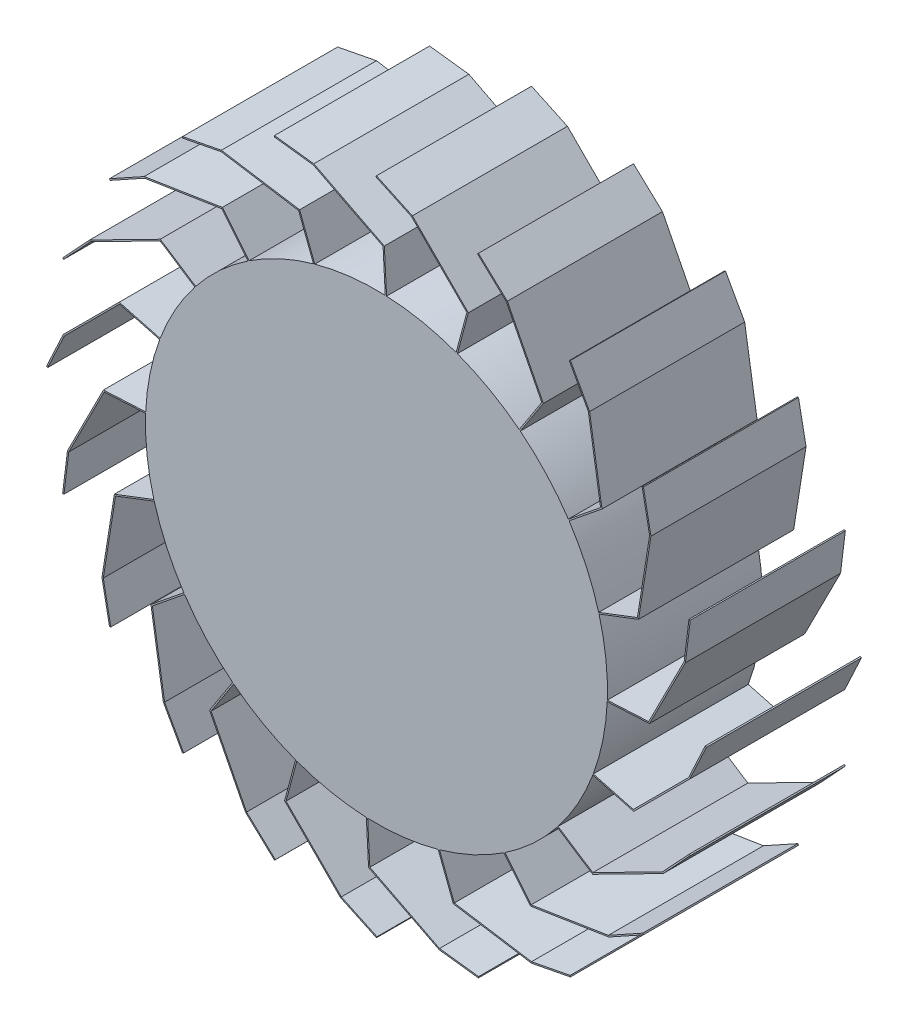
SolidWorks part; units mm, degrees
ref_plane "Front" through (0, 0, 0) normal (0, 0, 1) x (1, 0, 0)
ref_plane "Top" through (0, 0, 0) normal (0, 1, 0) x (1, 0, 0)
ref_plane "Right" through (0, 0, 0) normal (1, 0, 0) x (0, 0, -1)
sketch "Radbreite" plane through (0, 0, 0) normal (0, 1, 0) x (1, 0, 0)
  line L0 (-500, 0) -> (500, 0) construction
  line L2 (-500, -75) -> (500, -75) construction
  line L3 (-500, -75) -> (-500, 75) construction
  line L4 (-500, 75) -> (500, 75) construction
  line L5 (500, -75) -> (500, 75) construction
  line L6 (-500, -75) -> (500, 75) construction
  line L7 (-500, 75) -> (500, -75) construction
  point P0 (0, 0)
  point P4 (0, 0)
  point P10 (-500, 0)
sketch "Raddurchmesser" plane through (0, 0, 0) normal (0, 0, 1) x (1, 0, 0)
  circle A0 centre (0, 0) radius 500 construction
  circle A1 centre (0, 0) radius 350
  point P5 (0, 0)
ref_plane "Ebene1" through (0, 0, 75) normal (0, 0, 1) x (1, 0, 0)
ref_plane "Ebene2" through (0, 0, -75) normal (0, 0, -1) x (-1, 0, 0)
sketch "Schaufelschnitt" plane through (0, 0, 0) normal (0, 0, 1) x (1, 0, 0)
  line L0 (0, 500) -> (54.3785, 474.6429)
  line L1 (139.2313, 389.7901) -> (122.6253, 327.8156)
  line L2 (0, 0) -> (0, 500) construction
  line L3 (54.3785, 474.6429) -> (139.2313, 389.7901)
  line L4 (0, 0) -> (154.5085, 475.5283) construction
  line L5 (-0.8452, 498.1874) -> (53.2136, 472.9793)
  line L6 (53.2136, 472.9793) -> (137.0006, 389.1924)
  line L7 (137.0006, 389.1924) -> (120.6934, 328.3332)
  line L8 (0, 500) -> (-0.8452, 498.1874)
  line L9 (122.6253, 327.8156) -> (120.6934, 328.3332)
  line L10 (139.2313, 389.7901) -> (137.0006, 389.1924) construction
  line L11 (121.6593, 328.0744) -> (138.1159, 389.4912) construction
  line L23 (0, 0) -> (0, 500) construction
  line L61 (234.995, -415.957) -> (116.4724, -397.1849) [skipped]
  line L62 (94.9557, -468.2161) -> (-11.9651, -413.7372) [skipped]
  line L63 (154.5085, -475.5283) -> (94.9557, -468.2161) [skipped]
  line L64 (-54.3785, -474.6429) -> (-139.2313, -389.7901) [skipped]
  line L65 (0, -500) -> (-54.3785, -474.6429) [skipped]
  line L66 (-198.3897, -434.6084) -> (-252.8686, -327.6876) [skipped]
  line L67 (-154.5085, -475.5283) -> (-198.3897, -434.6084) [skipped]
  line L68 (-322.9812, -352.0313) -> (-341.7533, -233.5087) [skipped]
  line L69 (-293.8926, -404.5085) -> (-322.9812, -352.0313) [skipped]
  line L70 (-415.957, -234.995) -> (-397.1849, -116.4724) [skipped]
  line L71 (-404.5085, -293.8926) -> (-415.957, -234.995) [skipped]
  line L72 (-475.5283, -154.5085) -> (-468.2161, -94.9557) [skipped]
  line L73 (233.5087, -341.7533) -> (193.131, -291.8911) [skipped]
  line L74 (116.4724, -397.1849) -> (93.4792, -337.2857) [skipped]
  line L75 (-11.9651, -413.7372) -> (-15.323, -349.6644) [skipped]
  line L76 (-139.2313, -389.7901) -> (-122.6253, -327.8156) [skipped]
  line L77 (-252.8686, -327.6876) -> (-217.9241, -273.8778) [skipped]
  line L78 (-341.7533, -233.5087) -> (-291.8911, -193.131) [skipped]
  line L79 (-397.1849, -116.4724) -> (-337.2857, -93.4792) [skipped]
  line L80 (0, 0) -> (154.5085, -475.5283) construction
  line L81 (0, 0) -> (0, -500) construction
  line L82 (0, 0) -> (-154.5085, -475.5283) construction
  line L83 (0, 0) -> (-293.8926, -404.5085) construction
  line L84 (0, 0) -> (-404.5085, -293.8926) construction
  line L85 (0, 0) -> (-475.5283, -154.5085) construction
  line L86 (468.2161, 94.9557) -> (413.7372, -11.9651) [skipped]
  line L87 (475.5283, 154.5085) -> (468.2161, 94.9557) [skipped]
  line L88 (415.957, 234.995) -> (397.1849, 116.4724) [skipped]
  line L89 (404.5085, 293.8926) -> (415.957, 234.995) [skipped]
  line L90 (474.6429, -54.3785) -> (389.7901, -139.2313) [skipped]
  line L91 (500, 0) -> (474.6429, -54.3785) [skipped]
  line L92 (434.6084, -198.3897) -> (327.6876, -252.8686) [skipped]
  line L93 (475.5283, -154.5085) -> (434.6084, -198.3897) [skipped]
  line L94 (352.0313, -322.9812) -> (233.5087, -341.7533) [skipped]
  line L95 (404.5085, -293.8926) -> (352.0313, -322.9812) [skipped]
  line L96 (293.8926, -404.5085) -> (234.995, -415.957) [skipped]
  line L97 (341.7533, 233.5087) -> (291.8911, 193.131) [skipped]
  line L98 (397.1849, 116.4724) -> (337.2857, 93.4792) [skipped]
  line L99 (413.7372, -11.9651) -> (349.6644, -15.323) [skipped]
  line L100 (389.7901, -139.2313) -> (327.8156, -122.6253) [skipped]
  line L101 (327.6876, -252.8686) -> (273.8778, -217.9241) [skipped]
  line L102 (0, 0) -> (404.5085, 293.8926) construction
  line L103 (0, 0) -> (475.5283, 154.5085) construction
  line L104 (0, 0) -> (500, 0) construction
  line L105 (0, 0) -> (475.5283, -154.5085) construction
  line L106 (0, 0) -> (404.5085, -293.8926) construction
  line L107 (0, 0) -> (293.8926, -404.5085) construction
  line L108 (198.3897, 434.6084) -> (252.8686, 327.6876) [skipped]
  line L109 (154.5085, 475.5283) -> (198.3897, 434.6084) [skipped]
  line L110 (322.9812, 352.0313) -> (341.7533, 233.5087) [skipped]
  line L111 (293.8926, 404.5085) -> (322.9812, 352.0313) [skipped]
  line L112 (252.8686, 327.6876) -> (217.9241, 273.8778) [skipped]
  line L113 (-468.2161, -94.9557) -> (-413.7372, 11.9651) [skipped]
  line L114 (-413.7372, 11.9651) -> (-349.6644, 15.323) [skipped]
  line L115 (0, 0) -> (293.8926, 404.5085) construction
  line L116 (-474.6429, 54.3785) -> (-389.7901, 139.2313) [skipped]
  line L117 (-500, 0) -> (-474.6429, 54.3785) [skipped]
  line L118 (-389.7901, 139.2313) -> (-327.8156, 122.6253) [skipped]
  line L119 (-434.6084, 198.3897) -> (-327.6876, 252.8686) [skipped]
  line L120 (-475.5283, 154.5085) -> (-434.6084, 198.3897) [skipped]
  line L121 (-327.6876, 252.8686) -> (-273.8778, 217.9241) [skipped]
  line L122 (-352.0313, 322.9812) -> (-233.5087, 341.7533) [skipped]
  line L123 (-404.5085, 293.8926) -> (-352.0313, 322.9812) [skipped]
  line L124 (-233.5087, 341.7533) -> (-193.131, 291.8911) [skipped]
  line L125 (-234.995, 415.957) -> (-116.4724, 397.1849) [skipped]
  line L126 (-293.8926, 404.5085) -> (-234.995, 415.957) [skipped]
  line L127 (-116.4724, 397.1849) -> (-93.4792, 337.2857) [skipped]
  line L128 (-154.5085, 475.5283) -> (-94.9557, 468.2161) [skipped]
  line L129 (0, 0) -> (-404.5085, 293.8926) construction
  line L130 (0, 0) -> (-293.8926, 404.5085) construction
  line L131 (0, 0) -> (-475.5283, 154.5085) construction
  line L132 (0, 0) -> (-500, 0) construction
  line L133 (-94.9557, 468.2161) -> (11.9651, 413.7372) [skipped]
  line L134 (11.9651, 413.7372) -> (15.323, 349.6644) [skipped]
  line L135 (0, 0) -> (-154.5085, 475.5283) construction
  circle A0 centre (0, 0) radius 500 construction
  circle A1 centre (0, 0) radius 350 construction
sketch "Schaufelanordnung" plane through (0, 0, 0) normal (0, 0, 1) x (1, 0, 0)
  line L0 (139.2313, 389.7901) -> (122.6253, 327.8156) construction
  line L1 (0, 500) -> (54.3785, 474.6429) construction
  line L2 (54.3785, 474.6429) -> (139.2313, 389.7901) construction
  line L3 (139.2313, 389.7901) -> (122.6253, 327.8156)
  line L4 (0, 500) -> (54.3785, 474.6429)
  line L5 (54.3785, 474.6429) -> (139.2313, 389.7901)
  line L6 (252.8686, 327.6876) -> (217.9241, 273.8778)
  line L7 (198.3897, 434.6084) -> (252.8686, 327.6876)
  line L8 (154.5085, 475.5283) -> (198.3897, 434.6084)
  line L9 (341.7533, 233.5087) -> (291.8911, 193.131)
  line L10 (322.9812, 352.0313) -> (341.7533, 233.5087)
  line L11 (293.8926, 404.5085) -> (322.9812, 352.0313)
  line L12 (397.1849, 116.4724) -> (337.2857, 93.4792)
  line L13 (415.957, 234.995) -> (397.1849, 116.4724)
  line L14 (404.5085, 293.8926) -> (415.957, 234.995)
  line L15 (413.7372, -11.9651) -> (349.6644, -15.323)
  line L16 (468.2161, 94.9557) -> (413.7372, -11.9651)
  line L17 (475.5283, 154.5085) -> (468.2161, 94.9557)
  line L18 (389.7901, -139.2313) -> (327.8156, -122.6253)
  line L19 (474.6429, -54.3785) -> (389.7901, -139.2313)
  line L20 (500, 0) -> (474.6429, -54.3785)
  line L21 (327.6876, -252.8686) -> (273.8778, -217.9241)
  line L22 (434.6084, -198.3897) -> (327.6876, -252.8686)
  line L23 (475.5283, -154.5085) -> (434.6084, -198.3897)
  line L24 (233.5087, -341.7533) -> (193.131, -291.8911)
  line L25 (352.0313, -322.9812) -> (233.5087, -341.7533)
  line L26 (404.5085, -293.8926) -> (352.0313, -322.9812)
  line L27 (116.4724, -397.1849) -> (93.4792, -337.2857)
  line L28 (234.995, -415.957) -> (116.4724, -397.1849)
  line L29 (293.8926, -404.5085) -> (234.995, -415.957)
  line L30 (-11.9651, -413.7372) -> (-15.323, -349.6644)
  line L31 (94.9557, -468.2161) -> (-11.9651, -413.7372)
  line L32 (154.5085, -475.5283) -> (94.9557, -468.2161)
  line L33 (-139.2313, -389.7901) -> (-122.6253, -327.8156)
  line L34 (-54.3785, -474.6429) -> (-139.2313, -389.7901)
  line L35 (0, -500) -> (-54.3785, -474.6429)
  line L36 (-252.8686, -327.6876) -> (-217.9241, -273.8778)
  line L37 (-198.3897, -434.6084) -> (-252.8686, -327.6876)
  line L38 (-154.5085, -475.5283) -> (-198.3897, -434.6084)
  line L39 (-341.7533, -233.5087) -> (-291.8911, -193.131)
  line L40 (-322.9812, -352.0313) -> (-341.7533, -233.5087)
  line L41 (-293.8926, -404.5085) -> (-322.9812, -352.0313)
  line L42 (-397.1849, -116.4724) -> (-337.2857, -93.4792)
  line L43 (-415.957, -234.995) -> (-397.1849, -116.4724)
  line L44 (-404.5085, -293.8926) -> (-415.957, -234.995)
  line L45 (-413.7372, 11.9651) -> (-349.6644, 15.323)
  line L46 (-468.2161, -94.9557) -> (-413.7372, 11.9651)
  line L47 (-475.5283, -154.5085) -> (-468.2161, -94.9557)
  line L48 (-389.7901, 139.2313) -> (-327.8156, 122.6253)
  line L49 (-474.6429, 54.3785) -> (-389.7901, 139.2313)
  line L50 (-500, 0) -> (-474.6429, 54.3785)
  line L51 (-327.6876, 252.8686) -> (-273.8778, 217.9241)
  line L52 (-434.6084, 198.3897) -> (-327.6876, 252.8686)
  line L53 (-475.5283, 154.5085) -> (-434.6084, 198.3897)
  line L54 (-233.5087, 341.7533) -> (-193.131, 291.8911)
  line L55 (-352.0313, 322.9812) -> (-233.5087, 341.7533)
  line L56 (-404.5085, 293.8926) -> (-352.0313, 322.9812)
  line L57 (-116.4724, 397.1849) -> (-93.4792, 337.2857)
  line L58 (-234.995, 415.957) -> (-116.4724, 397.1849)
  line L59 (-293.8926, 404.5085) -> (-234.995, 415.957)
  line L60 (11.9651, 413.7372) -> (15.323, 349.6644)
  line L61 (-94.9557, 468.2161) -> (11.9651, 413.7372)
  line L62 (-154.5085, 475.5283) -> (-94.9557, 468.2161)
  line L63 (122.6253, 327.8156) -> (120.6934, 328.3332) construction
  line L64 (137.0006, 389.1924) -> (120.6934, 328.3332) construction
  line L65 (53.2136, 472.9793) -> (137.0006, 389.1924) construction
  line L66 (-0.8452, 498.1874) -> (53.2136, 472.9793) construction
  line L67 (0, 500) -> (-0.8452, 498.1874) construction
  line L68 (122.6253, 327.8156) -> (120.6934, 328.3332)
  line L69 (137.0006, 389.1924) -> (120.6934, 328.3332)
  line L70 (53.2136, 472.9793) -> (137.0006, 389.1924)
  line L71 (-0.8452, 498.1874) -> (53.2136, 472.9793)
  line L72 (0, 500) -> (-0.8452, 498.1874)
  line L73 (154.5085, 475.5283) -> (153.1445, 474.0656)
  line L74 (153.1445, 474.0656) -> (196.7678, 433.3862)
  line L75 (196.7678, 433.3862) -> (250.5623, 327.8084)
  line L76 (250.5623, 327.8084) -> (216.2468, 274.9671)
  line L78 (293.8926, 404.5085) -> (292.1434, 403.5389)
  line L79 (292.1434, 403.5389) -> (321.061, 351.3701)
  line L80 (321.061, 351.3701) -> (339.5973, 234.3363)
  line L81 (339.5973, 234.3363) -> (290.6324, 194.6853)
  line L83 (404.5085, 293.8926) -> (402.5452, 293.511)
  line L84 (402.5452, 293.511) -> (413.9265, 234.9596)
  line L85 (413.9265, 234.9596) -> (395.3902, 117.9257)
  line L86 (395.3902, 117.9257) -> (336.5689, 95.3464)
  line L88 (475.5283, 154.5085) -> (473.5432, 154.7522)
  line L89 (473.5432, 154.7522) -> (466.274, 95.5495)
  line L90 (466.274, 95.5495) -> (412.4794, -10.0282)
  line L91 (412.4794, -10.0282) -> (349.5597, -13.3257)
  line L93 (500, 0) -> (498.1874, 0.8452)
  line L94 (498.1874, 0.8452) -> (472.9793, -53.2136)
  line L95 (472.9793, -53.2136) -> (389.1924, -137.0006)
  line L96 (389.1924, -137.0006) -> (328.3332, -120.6934)
  line L98 (475.5283, -154.5085) -> (474.0656, -153.1445)
  line L99 (474.0656, -153.1445) -> (433.3862, -196.7678)
  line L100 (433.3862, -196.7678) -> (327.8084, -250.5623)
  line L101 (327.8084, -250.5623) -> (274.9671, -216.2468)
  line L103 (404.5085, -293.8926) -> (403.5389, -292.1434)
  line L104 (403.5389, -292.1434) -> (351.3701, -321.061)
  line L105 (351.3701, -321.061) -> (234.3363, -339.5973)
  line L106 (234.3363, -339.5973) -> (194.6853, -290.6324)
  line L108 (293.8926, -404.5085) -> (293.511, -402.5452)
  line L109 (293.511, -402.5452) -> (234.9596, -413.9265)
  line L110 (234.9596, -413.9265) -> (117.9257, -395.3902)
  line L111 (117.9257, -395.3902) -> (95.3464, -336.5689)
  line L113 (154.5085, -475.5283) -> (154.7522, -473.5432)
  line L114 (154.7522, -473.5432) -> (95.5495, -466.274)
  line L115 (95.5495, -466.274) -> (-10.0282, -412.4794)
  line L116 (-10.0282, -412.4794) -> (-13.3257, -349.5597)
  line L118 (0, -500) -> (0.8452, -498.1874)
  line L119 (0.8452, -498.1874) -> (-53.2136, -472.9793)
  line L120 (-53.2136, -472.9793) -> (-137.0006, -389.1924)
  line L121 (-137.0006, -389.1924) -> (-120.6934, -328.3332)
  line L123 (-154.5085, -475.5283) -> (-153.1445, -474.0656)
  line L124 (-153.1445, -474.0656) -> (-196.7678, -433.3862)
  line L125 (-196.7678, -433.3862) -> (-250.5623, -327.8084)
  line L126 (-250.5623, -327.8084) -> (-216.2468, -274.9671)
  line L128 (-293.8926, -404.5085) -> (-292.1434, -403.5389)
  line L129 (-292.1434, -403.5389) -> (-321.061, -351.3701)
  line L130 (-321.061, -351.3701) -> (-339.5973, -234.3363)
  line L131 (-339.5973, -234.3363) -> (-290.6324, -194.6853)
  line L133 (-404.5085, -293.8926) -> (-402.5452, -293.511)
  line L134 (-402.5452, -293.511) -> (-413.9265, -234.9596)
  line L135 (-413.9265, -234.9596) -> (-395.3902, -117.9257)
  line L136 (-395.3902, -117.9257) -> (-336.5689, -95.3464)
  line L138 (-475.5283, -154.5085) -> (-473.5432, -154.7522)
  line L139 (-473.5432, -154.7522) -> (-466.274, -95.5495)
  line L140 (-466.274, -95.5495) -> (-412.4794, 10.0282)
  line L141 (-412.4794, 10.0282) -> (-349.5597, 13.3257)
  line L143 (-500, 0) -> (-498.1874, -0.8452)
  line L144 (-498.1874, -0.8452) -> (-472.9793, 53.2136)
  line L145 (-472.9793, 53.2136) -> (-389.1924, 137.0006)
  line L146 (-389.1924, 137.0006) -> (-328.3332, 120.6934)
  line L148 (-475.5283, 154.5085) -> (-474.0656, 153.1445)
  line L149 (-474.0656, 153.1445) -> (-433.3862, 196.7678)
  line L150 (-433.3862, 196.7678) -> (-327.8084, 250.5623)
  line L151 (-327.8084, 250.5623) -> (-274.9671, 216.2468)
  line L153 (-404.5085, 293.8926) -> (-403.5389, 292.1434)
  line L154 (-403.5389, 292.1434) -> (-351.3701, 321.061)
  line L155 (-351.3701, 321.061) -> (-234.3363, 339.5973)
  line L156 (-234.3363, 339.5973) -> (-194.6853, 290.6324)
  line L158 (-293.8926, 404.5085) -> (-293.511, 402.5452)
  line L159 (-293.511, 402.5452) -> (-234.9596, 413.9265)
  line L160 (-234.9596, 413.9265) -> (-117.9257, 395.3902)
  line L161 (-117.9257, 395.3902) -> (-95.3464, 336.5689)
  line L163 (-154.5085, 475.5283) -> (-154.7522, 473.5432)
  line L164 (-154.7522, 473.5432) -> (-95.5495, 466.274)
  line L165 (-95.5495, 466.274) -> (10.0282, 412.4794)
  line L166 (10.0282, 412.4794) -> (13.3257, 349.5597)
  line L168 (121.6593, 328.0744) -> (138.1159, 389.4912) construction
  line L169 (121.6593, 328.0744) -> (138.1159, 389.4912) construction
  line L170 (217.0855, 274.4225) -> (251.7155, 327.748) construction
  line L171 (291.2618, 193.9082) -> (340.6753, 233.9225) construction
  line L172 (336.9273, 94.4128) -> (396.2875, 117.1991) construction
  line L173 (349.6121, -14.3243) -> (413.1083, -10.9966) construction
  line L174 (328.0744, -121.6593) -> (389.4912, -138.1159) construction
  line L175 (274.4225, -217.0855) -> (327.748, -251.7155) construction
  line L176 (193.9082, -291.2618) -> (233.9225, -340.6753) construction
  line L177 (94.4128, -336.9273) -> (117.1991, -396.2875) construction
  line L178 (-14.3243, -349.6121) -> (-10.9966, -413.1083) construction
  line L179 (-121.6593, -328.0744) -> (-138.1159, -389.4912) construction
  line L180 (-217.0855, -274.4225) -> (-251.7155, -327.748) construction
  line L181 (-291.2618, -193.9082) -> (-340.6753, -233.9225) construction
  line L182 (-336.9273, -94.4128) -> (-396.2875, -117.1991) construction
  line L183 (-349.6121, 14.3243) -> (-413.1083, 10.9966) construction
  line L184 (-328.0744, 121.6593) -> (-389.4912, 138.1159) construction
  line L185 (-274.4225, 217.0855) -> (-327.748, 251.7155) construction
  line L186 (-193.9082, 291.2618) -> (-233.9225, 340.6753) construction
  line L187 (-94.4128, 336.9273) -> (-117.1991, 396.2875) construction
  line L188 (14.3243, 349.6121) -> (10.9966, 413.1083) construction
  circle A0 centre (0, 0) radius 500 construction
  circle A1 centre (0, 0) radius 350 construction
  circle A2 centre (0, 0) radius 350
sketch "_Schottblechschnitt" plane through (0, 0, 0) normal (0, 0, 1) x (1, 0, 0)
  line L0 (14.3243, 349.6121) -> (10.9966, 413.1083) construction
  line L1 (15.3181, 349.6654) -> (121.448, 328.2544) construction
  line L2 (0, 0) -> (15.323, 349.6644) construction
  line L3 (-500, 0) -> (500, 0) construction
  line L4 (0, 0) -> (349.6644, -15.323) construction
  line L5 (121.6593, 328.0744) -> (138.1159, 389.4912) construction
  line L6 (14.9226, 347.7049) -> (121.0524, 326.2939) construction
  line L7 (0, 348.0917) -> (14.0677, 349.7179)
  line L8 (0, 0) -> (0, 500) construction
  line L9 (0, 348.0917) -> (0.2297, 346.105)
  line L10 (0.2297, 346.105) -> (14.2974, 347.7312)
  line L11 (108.1559, 332.8698) -> (107.5663, 331.0549) construction
  line L12 (0, 0) -> (154.5085, 475.5283) construction
  line L13 (0, 348.0917) -> (0, 350) construction
  line L14 (107.5663, 331.0549) -> (107.1707, 329.0944)
  line L15 (107.5663, 331.0549) -> (15.323, 349.6644)
  line L16 (14.9226, 347.7049) -> (107.1707, 329.0944)
  line L17 (134.8704, 306.085) -> (134.2514, 304.1832)
  line L18 (134.8704, 306.085) -> (148.3363, 301.7015)
  line L19 (134.2514, 304.1832) -> (147.7172, 299.7997)
  line L20 (225.5546, 245.7764) -> (149.4551, 301.1298)
  line L21 (148.2746, 299.5154) -> (224.3782, 244.159)
  line L22 (225.5546, 245.7764) -> (224.3782, 244.159)
  line L23 (239.9709, 211.7002) -> (238.6157, 210.2293)
  line L24 (239.9709, 211.7002) -> (250.3855, 202.1043)
  line L25 (238.6157, 210.2293) -> (249.0303, 200.6335)
  line L26 (297.2776, 119.0898) -> (251.1643, 201.1184)
  line L27 (249.4185, 200.1427) -> (295.5342, 118.1097)
  line L28 (297.2776, 119.0898) -> (295.5342, 118.1097)
  line L29 (296.1837, 82.1057) -> (294.3389, 81.3334)
  line L30 (296.1837, 82.1057) -> (301.6527, 69.043)
  line L31 (294.3389, 81.3334) -> (299.8078, 68.2706)
  line L32 (309.689, -25.9607) -> (301.9498, 67.8222)
  line L33 (299.9562, 67.6627) -> (307.6958, -26.1252)
  line L34 (309.689, -25.9607) -> (307.6958, -26.1252)
  line L35 (293.2838, -59.1253) -> (291.2849, -59.0587)
  line L36 (293.2838, -59.1253) -> (292.8123, -73.2788)
  line L37 (291.2849, -59.0587) -> (290.8134, -73.2122)
  line L38 (260.5311, -162.9906) -> (292.5738, -74.5123)
  line L39 (290.695, -73.8266) -> (258.6506, -162.3096)
  line L40 (260.5311, -162.9906) -> (258.6506, -162.3096)
  circle A0 centre (0, 0) radius 350 construction
  arc A1 (121.448, 328.2544) -> (124.0412, 326.4657) centre (120.6569, 324.3334) cw construction
  arc A2 (14.0677, 349.7179) -> (15.3181, 349.6654) centre (14.527, 345.7444) cw
  arc A3 (14.2974, 347.7312) -> (14.9226, 347.7049) centre (14.527, 345.7444) cw
  arc A4 (147.7172, 299.7997) -> (148.2746, 299.5154) centre (147.0982, 297.898) cw
  arc A5 (148.3363, 301.7015) -> (149.4511, 301.1327) centre (147.0982, 297.898) cw
  arc A6 (249.0303, 200.6335) -> (249.4185, 200.1427) centre (247.6751, 199.1626) cw
  arc A7 (250.3855, 202.1043) -> (251.1619, 201.1228) centre (247.6751, 199.1626) cw
  arc A8 (299.8078, 68.2706) -> (299.9562, 67.6627) centre (297.963, 67.4982) cw
  arc A9 (301.6527, 69.043) -> (301.9494, 67.8272) centre (297.963, 67.4982) cw
  arc A10 (290.8134, -73.2122) -> (290.695, -73.8266) centre (288.8145, -73.1456) cw
  arc A11 (292.8123, -73.2788) -> (292.5755, -74.5076) centre (288.8145, -73.1456) cw
  point P0 (122.6253, 327.8156)
  point P2 (15.323, 349.6644)
  point P4 (0, 0)
  point P27 (-10.1744, -10.348)
  point P40 (-23.7354, -15.5153)
  point P62 (-38.2161, -14.562)
  point P73 (-50.9825, -7.6615)
extrude "Aufsatz-Linear austragen1" add sketch "Raddurchmesser" along normal mid plane 235
extrude "Aufsatz-Linear austragen2" add sketch "Schaufelschnitt" along normal mid plane 235 contours L9 L1 L3 L0 L8 L5 L6 L7
pattern_circular "Kreismuster1" count 20 over 360 about axis through (0, 0, 0) along (0, 0, 1) of "Aufsatz-Linear austragen2"
equation "\"Durchmesser\"= 1000mm"
equation "\"Breite\"= 150mm"
equation "\"XX@Radbreite\" = \"Durchmesser\""
equation "\"D1@Radbreite\" = \"Breite\""
equation "\"D1@Raddurchmesser\" = \"Durchmesser\""
equation "\"Innenkreis\"= 700mm"
equation "\"D2@Raddurchmesser\" = \"Innenkreis\""
equation "\"Schaufelzahl\"= 20"
equation "\"Vollkreis\"= 360grad"
equation "\"SW1\"= 65grad'Schaufelwinkel aussen"
equation "\"SW2\"= 160grad'Schaufelwinkel mitte"
equation "\"SW3\"= 120grad'Schaufelwinkel innen"
equation "\"D3@Schaufelschnitt\" = \"SW2\""
equation "\"D4@Schaufelschnitt\" = \"SW3\""
equation "\"SL1\"= 60mm'Schaufellänge aussen"
equation "\"SL2\"= 120mm'Schaufellänge mitte"
equation "\"SL3\"= 30mm'Schaufellänge innen"
equation "\"D5@Schaufelschnitt\" = \"SL2\""
equation "\"D6@Schaufelschnitt\" = \"SL1\""
equation "\"STW\"= \"Vollkreis\" / \"Schaufelzahl\"'Schaufelteilungswinkel"
equation "\"D1@Schaufelschnitt\" = \"STW\""
equation "\"D7@Schaufelschnitt\" = \"Schaufelzahl\""
equation "\"D2@Schaufelschnitt\" = \"SW1\""
equation "\"D1@Schaufelanordnung\" = \"Schaufelzahl\""
equation "\"Schottblechzahl\"= 4"
equation "\"Schottblechwinkel\"= \"Vollkreis\" / \"Schottblechzahl\""
equation "\"D1@_Schottblechschnitt\" = \"Schottblechwinkel\""
equation "\"Schaufelstärke\"= 2mm"
equation "\"Schottblechstärke\"= 2mm"
equation "\"D8@Schaufelschnitt\"= \"Schaufelstärke\""
equation "\"D3@_Schottblechschnitt\" = \"D2@_Schottblechschnitt\""
equation "\"D2@_Schottblechschnitt\"=\"Schottblechstärke\"*2"
equation "\"D4@_Schottblechschnitt\"=\"Schottblechstärke\""
equation "\"D5@_Schottblechschnitt\"= \"Schaufelzahl\" / \"Schottblechzahl\""
